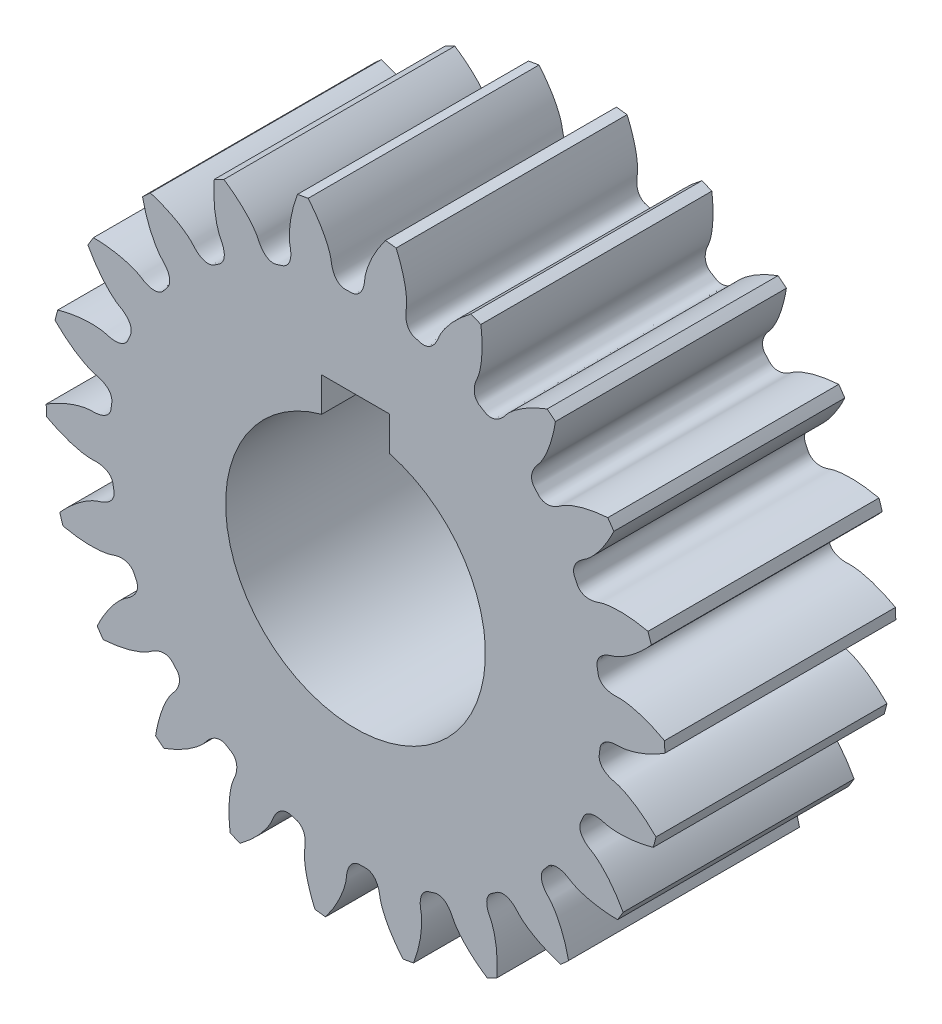
SolidWorks part; units mm, degrees
ref_plane "Front Plane" through (0, 0, 0) normal (0, 0, 1) x (1, 0, 0)
ref_plane "Top Plane" through (0, 0, 0) normal (0, 1, 0) x (1, 0, 0)
ref_plane "Right Plane" through (0, 0, 0) normal (1, 0, 0) x (0, 0, -1)
sketch "Sketch1" plane through (0, 0, 0) normal (0, 0, 1) x (1, 0, 0)
  line L0 (0, -4) -> (0, 4.9154) construction
  line L1 (-1.0414, 4.9154) -> (1.0414, 4.9154)
  line L2 (-1.0414, 4.9154) -> (-1.0414, 3.8621)
  line L3 (1.0414, 4.9154) -> (1.0414, 3.8621)
  arc A1 (-1.4616, 9.4122) -> (-1.7864, 9.356) centre (0, 0) ccw
  arc A20 (-1.0414, 3.8621) -> (1.0414, 3.8621) centre (0, 0) ccw
  arc A22 (1.2494, 9.4427) -> (0.9219, 9.4803) centre (0, 0) ccw
  arc A23 (3.8591, 8.7082) -> (3.5554, 8.8366) centre (0, 0) ccw
  arc A24 (6.1561, 7.2683) -> (5.9009, 7.4769) centre (0, 0) ccw
  arc A25 (7.9545, 5.2395) -> (7.7684, 5.5116) centre (0, 0) ccw
  arc A26 (9.1084, 2.7862) -> (9.0065, 3.0997) centre (0, 0) ccw
  arc A27 (9.5244, 0.1072) -> (9.515, 0.4367) centre (0, 0) ccw
  arc A28 (9.1688, -2.5805) -> (9.2526, -2.2617) centre (0, 0) ccw
  arc A29 (8.0704, -5.0591) -> (8.2406, -4.7768) centre (0, 0) ccw
  arc A30 (6.3182, -7.1279) -> (6.561, -6.905) centre (0, 0) ccw
  arc A31 (4.0541, -8.6192) -> (4.3499, -8.4737) centre (0, 0) ccw
  arc A32 (1.4616, -9.4122) -> (1.7864, -9.356) centre (0, 0) ccw
  arc A33 (-1.2494, -9.4427) -> (-0.9219, -9.4803) centre (0, 0) ccw
  arc A34 (-3.8591, -8.7082) -> (-3.5554, -8.8366) centre (0, 0) ccw
  arc A35 (-6.1561, -7.2683) -> (-5.9009, -7.4769) centre (0, 0) ccw
  arc A36 (-7.9545, -5.2395) -> (-7.7684, -5.5116) centre (0, 0) ccw
  arc A37 (-9.1084, -2.7862) -> (-9.0065, -3.0997) centre (0, 0) ccw
  arc A38 (-9.5244, -0.1072) -> (-9.515, -0.4367) centre (0, 0) ccw
  arc A39 (-9.1688, 2.5805) -> (-9.2526, 2.2617) centre (0, 0) ccw
  arc A40 (-8.0704, 5.0591) -> (-8.2406, 4.7768) centre (0, 0) ccw
  arc A41 (-6.3182, 7.1279) -> (-6.561, 6.905) centre (0, 0) ccw
  arc A42 (-4.0541, 8.6192) -> (-4.3499, 8.4737) centre (0, 0) ccw
  spline S0 degree 3 poles (0.9219, 9.4803) (0.8728, 9.4149) (0.7991, 9.3114) (0.7064, 9.1689) (0.6396, 9.0591) (0.5802, 8.954) (0.5276, 8.8541) (0.4816, 8.7596) (0.4417, 8.6708) (0.4075, 8.588) (0.3787, 8.5115) (0.3547, 8.4415) (0.3352, 8.3782) (0.3197, 8.3219) (0.3078, 8.2727) (0.299, 8.2308) (0.2929, 8.1963) (0.2845, 8.1391) (0.282, 8.0848) (0.2743, 8.0322) (0.2704, 8.0084) (0.2632, 7.9701) (0.2525, 7.9254) (0.2368, 7.875) (0.221, 7.8334) (0.2024, 7.7931) (0.1806, 7.7538) (0.1547, 7.7156) (0.1237, 7.6787) (0.0864, 7.6435) (0.0417, 7.6116) (-0.0017, 7.5901) (-0.0401, 7.5768) (-0.0711, 7.5693) (-0.1009, 7.565) (-0.1493, 7.5621) (-0.216, 7.5625) (-0.2826, 7.5583) (-0.3311, 7.5584) (-0.3611, 7.561) (-0.3925, 7.5667) (-0.4317, 7.5778) (-0.4761, 7.5968) (-0.5227, 7.6261) (-0.5619, 7.6591) (-0.5949, 7.6942) (-0.6229, 7.7309) (-0.647, 7.7688) (-0.6713, 7.8146) (-0.6948, 7.8696) (-0.7113, 7.9198) (-0.7214, 7.9569) (-0.7272, 7.9799) (-0.7324, 8.0034) (-0.7431, 8.0555) (-0.7487, 8.1096) (-0.7604, 8.1662) (-0.7684, 8.2003) (-0.7796, 8.2417) (-0.7943, 8.2901) (-0.813, 8.3454) (-0.836, 8.4075) (-0.8639, 8.476) (-0.8971, 8.5507) (-0.936, 8.6314) (-0.9809, 8.7178) (-1.0322, 8.8095) (-1.0904, 8.9063) (-1.1558, 9.0078) (-1.2286, 9.1136) (-1.3293, 9.2506) (-1.4089, 9.3497) (-1.4616, 9.4122) knots -1.711873 -1.711873 -1.711873 -1.711873 -1.623296 -1.57405 -1.527618 -1.484001 -1.443197 -1.405207 -1.370031 -1.337669 -1.308122 -1.281388 -1.257469 -1.236363 -1.218072 -1.202595 -1.189931 -1.180082 -1.139962 -1.131119 -1.122418 -1.11385 -1.088841 -1.072621 -1.056613 -1.04065 -1.024521 -1.007966 -0.990676 -0.97231 -0.952557 -0.931244 -0.920025 -0.908493 -0.896727 -0.887452 -0.855936 -0.82442 -0.815146 -0.803379 -0.791848 -0.780629 -0.759316 -0.739562 -0.721197 -0.703907 -0.687352 -0.671223 -0.655259 -0.631177 -0.606467 -0.598023 -0.589455 -0.580754 -0.57191 -0.531791 -0.521942 -0.509278 -0.493801 -0.47551 -0.454404 -0.430485 -0.403751 -0.374203 -0.341842 -0.306666 -0.268676 -0.227872 -0.184254 -0.137822 -0.088576 0 0 0 0
  spline S1 degree 3 poles (-1.7864, 9.356) (-1.815, 9.2795) (-1.8566, 9.1593) (-1.9054, 8.9965) (-1.9385, 8.8723) (-1.966, 8.7548) (-1.9882, 8.6441) (-2.0058, 8.5404) (-2.0191, 8.444) (-2.0285, 8.3549) (-2.0347, 8.2734) (-2.0379, 8.1995) (-2.0388, 8.1333) (-2.0378, 8.0749) (-2.0353, 8.0243) (-2.032, 7.9816) (-2.0281, 7.9468) (-2.0201, 7.8896) (-2.0072, 7.8368) (-1.9997, 7.7841) (-1.9968, 7.7602) (-1.9929, 7.7214) (-1.9905, 7.6755) (-1.9914, 7.6227) (-1.9949, 7.5784) (-2.0013, 7.5344) (-2.0112, 7.4906) (-2.0253, 7.4467) (-2.0446, 7.4025) (-2.0705, 7.3583) (-2.1045, 7.3151) (-2.14, 7.2821) (-2.1731, 7.2586) (-2.2007, 7.2426) (-2.2281, 7.2301) (-2.2738, 7.2138) (-2.3379, 7.1953) (-2.4006, 7.1725) (-2.4472, 7.159) (-2.4767, 7.153) (-2.5084, 7.1497) (-2.5491, 7.1492) (-2.5971, 7.155) (-2.65, 7.17) (-2.6969, 7.1905) (-2.7385, 7.215) (-2.7757, 7.2422) (-2.8095, 7.2718) (-2.8458, 7.3089) (-2.8838, 7.3551) (-2.9137, 7.3986) (-2.9339, 7.4313) (-2.9459, 7.4518) (-2.9576, 7.4729) (-2.9825, 7.5199) (-3.0031, 7.5702) (-3.0302, 7.6212) (-3.0476, 7.6516) (-3.07, 7.6882) (-3.0977, 7.7305) (-3.1312, 7.7784) (-3.1708, 7.8314) (-3.2169, 7.8893) (-3.2698, 7.9516) (-3.3298, 8.0181) (-3.3972, 8.0883) (-3.4723, 8.1619) (-3.5554, 8.2383) (-3.6467, 8.3173) (-3.7465, 8.3983) (-3.8817, 8.5013) (-3.986, 8.5741) (-4.0541, 8.6192) knots -1.711873 -1.711873 -1.711873 -1.711873 -1.623296 -1.57405 -1.527618 -1.484001 -1.443197 -1.405207 -1.370031 -1.337669 -1.308122 -1.281388 -1.257469 -1.236363 -1.218072 -1.202595 -1.189931 -1.180082 -1.139962 -1.131119 -1.122418 -1.11385 -1.088841 -1.072621 -1.056613 -1.04065 -1.024521 -1.007966 -0.990676 -0.97231 -0.952557 -0.931244 -0.920025 -0.908493 -0.896727 -0.887452 -0.855936 -0.82442 -0.815146 -0.803379 -0.791848 -0.780629 -0.759316 -0.739562 -0.721197 -0.703907 -0.687352 -0.671223 -0.655259 -0.631177 -0.606467 -0.598023 -0.589455 -0.580754 -0.57191 -0.531791 -0.521942 -0.509278 -0.493801 -0.47551 -0.454404 -0.430485 -0.403751 -0.374203 -0.341842 -0.306666 -0.268676 -0.227872 -0.184254 -0.137822 -0.088576 0 0 0 0
  spline S2 degree 3 poles (3.5554, 8.8366) (3.49, 8.7877) (3.39, 8.7091) (3.2609, 8.5985) (3.166, 8.5119) (3.0793, 8.4279) (3.0007, 8.3468) (2.9299, 8.2691) (2.8666, 8.1951) (2.8105, 8.1253) (2.7613, 8.06) (2.7186, 7.9996) (2.682, 7.9444) (2.6513, 7.8948) (2.6261, 7.8509) (2.6058, 7.8132) (2.5902, 7.7818) (2.566, 7.7293) (2.5483, 7.6779) (2.5261, 7.6295) (2.5157, 7.6078) (2.4979, 7.5731) (2.4751, 7.5332) (2.4458, 7.4893) (2.419, 7.4538) (2.3898, 7.4204) (2.3578, 7.3889) (2.3222, 7.3595) (2.282, 7.3328) (2.2364, 7.3096) (2.1844, 7.2916) (2.1368, 7.2831) (2.0961, 7.2812) (2.0643, 7.2827) (2.0345, 7.287) (1.9872, 7.2979) (1.9233, 7.317) (1.8582, 7.3318) (1.8117, 7.3456) (1.7837, 7.3564) (1.7552, 7.3708) (1.7207, 7.3924) (1.6834, 7.4233) (1.647, 7.4645) (1.6187, 7.5071) (1.5969, 7.5502) (1.5803, 7.5932) (1.5679, 7.6364) (1.5575, 7.6872) (1.5505, 7.7466) (1.5488, 7.7994) (1.5495, 7.8378) (1.5505, 7.8615) (1.5521, 7.8856) (1.5565, 7.9386) (1.5664, 7.9921) (1.5711, 8.0496) (1.573, 8.0846) (1.5739, 8.1275) (1.5735, 8.1781) (1.5712, 8.2364) (1.5665, 8.3025) (1.559, 8.3761) (1.5482, 8.4571) (1.5337, 8.5455) (1.515, 8.641) (1.4915, 8.7435) (1.463, 8.8527) (1.4288, 8.9685) (1.3887, 9.0906) (1.3307, 9.2504) (1.2823, 9.3679) (1.2494, 9.4427) knots -1.711873 -1.711873 -1.711873 -1.711873 -1.623296 -1.57405 -1.527618 -1.484001 -1.443197 -1.405207 -1.370031 -1.337669 -1.308122 -1.281388 -1.257469 -1.236363 -1.218072 -1.202595 -1.189931 -1.180082 -1.139962 -1.131119 -1.122418 -1.11385 -1.088841 -1.072621 -1.056613 -1.04065 -1.024521 -1.007966 -0.990676 -0.97231 -0.952557 -0.931244 -0.920025 -0.908493 -0.896727 -0.887452 -0.855936 -0.82442 -0.815146 -0.803379 -0.791848 -0.780629 -0.759316 -0.739562 -0.721197 -0.703907 -0.687352 -0.671223 -0.655259 -0.631177 -0.606467 -0.598023 -0.589455 -0.580754 -0.57191 -0.531791 -0.521942 -0.509278 -0.493801 -0.47551 -0.454404 -0.430485 -0.403751 -0.374203 -0.341842 -0.306666 -0.268676 -0.227872 -0.184254 -0.137822 -0.088576 0 0 0 0
  spline S3 degree 3 poles (5.9009, 7.4769) (5.8244, 7.4485) (5.7063, 7.4012) (5.5513, 7.3315) (5.4358, 7.2752) (5.329, 7.2189) (5.2307, 7.1633) (5.1409, 7.1087) (5.0593, 7.0555) (4.9858, 7.0044) (4.9202, 6.9556) (4.8622, 6.9097) (4.8116, 6.867) (4.7681, 6.828) (4.7315, 6.793) (4.7015, 6.7625) (4.6777, 6.7368) (4.6397, 6.6933) (4.6082, 6.6489) (4.5733, 6.6088) (4.5572, 6.5909) (4.5304, 6.5626) (4.4972, 6.5307) (4.4567, 6.4968) (4.421, 6.4704) (4.3835, 6.4465) (4.344, 6.4253) (4.3015, 6.4072) (4.2555, 6.3928) (4.2051, 6.3834) (4.1502, 6.3808) (4.1021, 6.3861) (4.0626, 6.3957) (4.0324, 6.4061) (4.0051, 6.4187) (3.9628, 6.4424) (3.9068, 6.4788) (3.8486, 6.5113) (3.8078, 6.5376) (3.784, 6.5559) (3.7607, 6.5777) (3.7337, 6.6082) (3.7066, 6.6483) (3.6833, 6.6981) (3.6681, 6.747) (3.6594, 6.7944) (3.6556, 6.8404) (3.6558, 6.8853) (3.6601, 6.937) (3.6701, 6.996) (3.6834, 7.0471) (3.6949, 7.0838) (3.7025, 7.1063) (3.7108, 7.1289) (3.73, 7.1785) (3.7546, 7.227) (3.7753, 7.2809) (3.787, 7.314) (3.7999, 7.3548) (3.8138, 7.4035) (3.828, 7.4602) (3.8421, 7.5248) (3.8557, 7.5976) (3.8682, 7.6784) (3.8791, 7.7672) (3.888, 7.8642) (3.8944, 7.9691) (3.8978, 8.082) (3.8977, 8.2027) (3.8936, 8.3311) (3.8829, 8.5007) (3.8696, 8.6272) (3.8591, 8.7082) knots -1.711873 -1.711873 -1.711873 -1.711873 -1.623296 -1.57405 -1.527618 -1.484001 -1.443197 -1.405207 -1.370031 -1.337669 -1.308122 -1.281388 -1.257469 -1.236363 -1.218072 -1.202595 -1.189931 -1.180082 -1.139962 -1.131119 -1.122418 -1.11385 -1.088841 -1.072621 -1.056613 -1.04065 -1.024521 -1.007966 -0.990676 -0.97231 -0.952557 -0.931244 -0.920025 -0.908493 -0.896727 -0.887452 -0.855936 -0.82442 -0.815146 -0.803379 -0.791848 -0.780629 -0.759316 -0.739562 -0.721197 -0.703907 -0.687352 -0.671223 -0.655259 -0.631177 -0.606467 -0.598023 -0.589455 -0.580754 -0.57191 -0.531791 -0.521942 -0.509278 -0.493801 -0.47551 -0.454404 -0.430485 -0.403751 -0.374203 -0.341842 -0.306666 -0.268676 -0.227872 -0.184254 -0.137822 -0.088576 0 0 0 0
  spline S4 degree 3 poles (7.7684, 5.5116) (7.6869, 5.5058) (7.5603, 5.4938) (7.392, 5.4705) (7.2653, 5.449) (7.1469, 5.4252) (7.037, 5.3995) (6.9354, 5.3723) (6.8422, 5.3444) (6.7572, 5.316) (6.6805, 5.2877) (6.6119, 5.2599) (6.5514, 5.2333) (6.4987, 5.2081) (6.4537, 5.1848) (6.4163, 5.164) (6.3862, 5.1461) (6.3374, 5.115) (6.2948, 5.0813) (6.25, 5.0526) (6.2294, 5.04) (6.1957, 5.0204) (6.155, 4.9992) (6.1066, 4.9781) (6.0648, 4.9628) (6.0222, 4.9504) (5.9782, 4.9412) (5.9324, 4.9358) (5.8842, 4.935) (5.8332, 4.9401) (5.7798, 4.9531) (5.7351, 4.9717) (5.6999, 4.9921) (5.6739, 5.0106) (5.6512, 5.0303) (5.6173, 5.065) (5.5739, 5.1156) (5.5271, 5.1633) (5.4954, 5.2) (5.4777, 5.2243) (5.4615, 5.2518) (5.4442, 5.2886) (5.4295, 5.3347) (5.4212, 5.3891) (5.4204, 5.4403) (5.4253, 5.4882) (5.4347, 5.5334) (5.4476, 5.5765) (5.4663, 5.6248) (5.4924, 5.6786) (5.5196, 5.7239) (5.541, 5.7559) (5.5546, 5.7753) (5.569, 5.7947) (5.6014, 5.8368) (5.6386, 5.8765) (5.6737, 5.9224) (5.6942, 5.9508) (5.7181, 5.9863) (5.7451, 6.0292) (5.7747, 6.0795) (5.8065, 6.1376) (5.84, 6.2035) (5.8747, 6.2775) (5.9103, 6.3597) (5.9461, 6.4502) (5.9818, 6.5491) (6.0169, 6.6565) (6.0508, 6.7723) (6.083, 6.8967) (6.1206, 7.0625) (6.1434, 7.1876) (6.1561, 7.2683) knots -1.711873 -1.711873 -1.711873 -1.711873 -1.623296 -1.57405 -1.527618 -1.484001 -1.443197 -1.405207 -1.370031 -1.337669 -1.308122 -1.281388 -1.257469 -1.236363 -1.218072 -1.202595 -1.189931 -1.180082 -1.139962 -1.131119 -1.122418 -1.11385 -1.088841 -1.072621 -1.056613 -1.04065 -1.024521 -1.007966 -0.990676 -0.97231 -0.952557 -0.931244 -0.920025 -0.908493 -0.896727 -0.887452 -0.855936 -0.82442 -0.815146 -0.803379 -0.791848 -0.780629 -0.759316 -0.739562 -0.721197 -0.703907 -0.687352 -0.671223 -0.655259 -0.631177 -0.606467 -0.598023 -0.589455 -0.580754 -0.57191 -0.531791 -0.521942 -0.509278 -0.493801 -0.47551 -0.454404 -0.430485 -0.403751 -0.374203 -0.341842 -0.306666 -0.268676 -0.227872 -0.184254 -0.137822 -0.088576 0 0 0 0
  spline S5 degree 3 poles (9.0065, 3.0997) (8.9267, 3.1171) (8.8018, 3.1412) (8.6338, 3.1664) (8.5061, 3.1814) (8.3859, 3.1919) (8.2731, 3.1982) (8.168, 3.2008) (8.0707, 3.2002) (7.9812, 3.1969) (7.8996, 3.1914) (7.826, 3.1841) (7.7604, 3.1755) (7.7027, 3.1662) (7.653, 3.1566) (7.6112, 3.1472) (7.5773, 3.1384) (7.5218, 3.1223) (7.4714, 3.1021) (7.4203, 3.0872) (7.397, 3.0808) (7.3592, 3.0715) (7.3141, 3.0626) (7.2617, 3.056) (7.2173, 3.0531) (7.1729, 3.0532) (7.1282, 3.0568) (7.0827, 3.0645) (7.0362, 3.0773) (6.9887, 3.0966) (6.9411, 3.1241) (6.9035, 3.1545) (6.8754, 3.184) (6.8557, 3.2091) (6.8395, 3.2344) (6.8167, 3.2773) (6.7893, 3.3381) (6.7579, 3.3969) (6.7378, 3.4411) (6.7277, 3.4694) (6.7199, 3.5003) (6.7137, 3.5406) (6.7125, 3.589) (6.7199, 3.6434) (6.7335, 3.6928) (6.7518, 3.7374) (6.7735, 3.7782) (6.798, 3.8158) (6.8295, 3.857) (6.8698, 3.9011) (6.9086, 3.937) (6.9382, 3.9617) (6.9567, 3.9764) (6.9759, 3.991) (7.0189, 4.0223) (7.0658, 4.0499) (7.1124, 4.084) (7.14, 4.1055) (7.173, 4.1329) (7.211, 4.1663) (7.2536, 4.2063) (7.3004, 4.2531) (7.3511, 4.3069) (7.4053, 4.3682) (7.4626, 4.437) (7.5225, 4.5137) (7.5846, 4.5986) (7.6485, 4.6917) (7.7137, 4.7933) (7.7796, 4.9035) (7.8624, 5.052) (7.9196, 5.1656) (7.9545, 5.2395) knots -1.711873 -1.711873 -1.711873 -1.711873 -1.623296 -1.57405 -1.527618 -1.484001 -1.443197 -1.405207 -1.370031 -1.337669 -1.308122 -1.281388 -1.257469 -1.236363 -1.218072 -1.202595 -1.189931 -1.180082 -1.139962 -1.131119 -1.122418 -1.11385 -1.088841 -1.072621 -1.056613 -1.04065 -1.024521 -1.007966 -0.990676 -0.97231 -0.952557 -0.931244 -0.920025 -0.908493 -0.896727 -0.887452 -0.855936 -0.82442 -0.815146 -0.803379 -0.791848 -0.780629 -0.759316 -0.739562 -0.721197 -0.703907 -0.687352 -0.671223 -0.655259 -0.631177 -0.606467 -0.598023 -0.589455 -0.580754 -0.57191 -0.531791 -0.521942 -0.509278 -0.493801 -0.47551 -0.454404 -0.430485 -0.403751 -0.374203 -0.341842 -0.306666 -0.268676 -0.227872 -0.184254 -0.137822 -0.088576 0 0 0 0
  spline S6 degree 3 poles (9.515, 0.4367) (9.4433, 0.4759) (9.3303, 0.5342) (9.1761, 0.6057) (9.0579, 0.6561) (8.9455, 0.7) (8.8391, 0.7378) (8.739, 0.7699) (8.6454, 0.7968) (8.5586, 0.8188) (8.4788, 0.8365) (8.4061, 0.8503) (8.3407, 0.8606) (8.2827, 0.8679) (8.2323, 0.8726) (8.1896, 0.8754) (8.1546, 0.8765) (8.0968, 0.8767) (8.0427, 0.8715) (7.9895, 0.8716) (7.9654, 0.8721) (7.9264, 0.8738) (7.8807, 0.8779) (7.8285, 0.8863) (7.7851, 0.8961) (7.7426, 0.9087) (7.7006, 0.9247) (7.6591, 0.945) (7.6181, 0.9703) (7.578, 1.0022) (7.5401, 1.042) (7.5126, 1.0818) (7.494, 1.118) (7.4821, 1.1476) (7.4737, 1.1765) (7.4639, 1.224) (7.4547, 1.2901) (7.4412, 1.3554) (7.4344, 1.4034) (7.4326, 1.4335) (7.4339, 1.4653) (7.4392, 1.5057) (7.4518, 1.5524) (7.4741, 1.6027) (7.5012, 1.6462) (7.5313, 1.6838) (7.5635, 1.7168) (7.5977, 1.746) (7.6395, 1.7766) (7.6906, 1.8077) (7.738, 1.8311) (7.7732, 1.8465) (7.7952, 1.8554) (7.8177, 1.864) (7.8678, 1.8819) (7.9205, 1.8952) (7.9749, 1.9148) (8.0075, 1.9276) (8.0468, 1.9446) (8.0927, 1.966) (8.1448, 1.9924) (8.2029, 2.024) (8.2668, 2.0614) (8.336, 2.1049) (8.4104, 2.1548) (8.4895, 2.2116) (8.573, 2.2754) (8.6605, 2.3468) (8.7516, 2.4259) (8.846, 2.5131) (8.9672, 2.6323) (9.0541, 2.7252) (9.1084, 2.7862) knots -1.711873 -1.711873 -1.711873 -1.711873 -1.623296 -1.57405 -1.527618 -1.484001 -1.443197 -1.405207 -1.370031 -1.337669 -1.308122 -1.281388 -1.257469 -1.236363 -1.218072 -1.202595 -1.189931 -1.180082 -1.139962 -1.131119 -1.122418 -1.11385 -1.088841 -1.072621 -1.056613 -1.04065 -1.024521 -1.007966 -0.990676 -0.97231 -0.952557 -0.931244 -0.920025 -0.908493 -0.896727 -0.887452 -0.855936 -0.82442 -0.815146 -0.803379 -0.791848 -0.780629 -0.759316 -0.739562 -0.721197 -0.703907 -0.687352 -0.671223 -0.655259 -0.631177 -0.606467 -0.598023 -0.589455 -0.580754 -0.57191 -0.531791 -0.521942 -0.509278 -0.493801 -0.47551 -0.454404 -0.430485 -0.403751 -0.374203 -0.341842 -0.306666 -0.268676 -0.227872 -0.184254 -0.137822 -0.088576 0 0 0 0
  spline S7 degree 3 poles (9.2526, -2.2617) (9.1949, -2.2038) (9.1029, -2.1161) (8.975, -2.004) (8.8758, -1.9224) (8.7803, -1.8486) (8.6889, -1.7823) (8.6019, -1.7233) (8.5197, -1.6712) (8.4426, -1.6256) (8.371, -1.5861) (8.3051, -1.5524) (8.2453, -1.5241) (8.1917, -1.5008) (8.1447, -1.482) (8.1045, -1.4674) (8.0712, -1.4564) (8.0158, -1.4399) (7.9624, -1.4297) (7.9114, -1.4146) (7.8884, -1.4074) (7.8515, -1.3948) (7.8088, -1.3779) (7.7611, -1.3551) (7.7222, -1.3335) (7.6849, -1.3094) (7.6492, -1.2822) (7.6151, -1.2512) (7.5829, -1.2152) (7.5534, -1.1733) (7.5282, -1.1245) (7.513, -1.0785) (7.5054, -1.0386) (7.5023, -1.0068) (7.5024, -0.9767) (7.5064, -0.9284) (7.5162, -0.8624) (7.5216, -0.7959) (7.5286, -0.7479) (7.5354, -0.7186) (7.5456, -0.6884) (7.5621, -0.6512) (7.5873, -0.6098) (7.6229, -0.568) (7.6611, -0.5339) (7.7006, -0.5062) (7.7408, -0.4836) (7.7818, -0.4652) (7.8306, -0.4476) (7.8884, -0.4322) (7.9404, -0.4231) (7.9786, -0.4183) (8.0022, -0.4159) (8.0262, -0.414) (8.0793, -0.4109) (8.1336, -0.4131) (8.1913, -0.4096) (8.2262, -0.4064) (8.2687, -0.4012) (8.3188, -0.3936) (8.3762, -0.383) (8.4409, -0.369) (8.5127, -0.3511) (8.5914, -0.3289) (8.6768, -0.3019) (8.7687, -0.2698) (8.8668, -0.232) (8.9708, -0.1882) (9.0806, -0.1379) (9.1957, -0.0809) (9.3456, -0.0007) (9.4551, 0.0639) (9.5244, 0.1072) knots -1.711873 -1.711873 -1.711873 -1.711873 -1.623296 -1.57405 -1.527618 -1.484001 -1.443197 -1.405207 -1.370031 -1.337669 -1.308122 -1.281388 -1.257469 -1.236363 -1.218072 -1.202595 -1.189931 -1.180082 -1.139962 -1.131119 -1.122418 -1.11385 -1.088841 -1.072621 -1.056613 -1.04065 -1.024521 -1.007966 -0.990676 -0.97231 -0.952557 -0.931244 -0.920025 -0.908493 -0.896727 -0.887452 -0.855936 -0.82442 -0.815146 -0.803379 -0.791848 -0.780629 -0.759316 -0.739562 -0.721197 -0.703907 -0.687352 -0.671223 -0.655259 -0.631177 -0.606467 -0.598023 -0.589455 -0.580754 -0.57191 -0.531791 -0.521942 -0.509278 -0.493801 -0.47551 -0.454404 -0.430485 -0.403751 -0.374203 -0.341842 -0.306666 -0.268676 -0.227872 -0.184254 -0.137822 -0.088576 0 0 0 0
  spline S8 degree 3 poles (8.2406, -4.7768) (8.2015, -4.7051) (8.138, -4.5949) (8.0469, -4.4514) (7.9747, -4.3451) (7.9039, -4.2474) (7.8348, -4.1581) (7.7679, -4.0769) (7.7037, -4.0037) (7.6426, -3.9383) (7.585, -3.8802) (7.5313, -3.8294) (7.4819, -3.7854) (7.4371, -3.7479) (7.3973, -3.7166) (7.3628, -3.6912) (7.3339, -3.6713) (7.2854, -3.6399) (7.2371, -3.6151) (7.1924, -3.5862) (7.1724, -3.5728) (7.1405, -3.5503) (7.1043, -3.522) (7.065, -3.4868) (7.0337, -3.4551) (7.0047, -3.4215) (6.9781, -3.3853) (6.9541, -3.3459) (6.9334, -3.3024) (6.9169, -3.2539) (6.9065, -3.1999) (6.9048, -3.1515) (6.9088, -3.111) (6.9148, -3.0797) (6.9233, -3.0508) (6.9408, -3.0056) (6.9688, -2.945) (6.9927, -2.8827) (7.013, -2.8387) (7.0277, -2.8125) (7.046, -2.7863) (7.0723, -2.7553) (7.1081, -2.7227) (7.1541, -2.6926) (7.2004, -2.6706) (7.2461, -2.6552) (7.291, -2.6449) (7.3355, -2.6388) (7.3873, -2.6356) (7.4471, -2.6371) (7.4996, -2.643) (7.5375, -2.6492) (7.5609, -2.6535) (7.5844, -2.6585) (7.6363, -2.6705) (7.6878, -2.6878) (7.7441, -2.7007) (7.7785, -2.7075) (7.8207, -2.7146) (7.8709, -2.7213) (7.929, -2.7273) (7.995, -2.7321) (8.0689, -2.7352) (8.1507, -2.7361) (8.2402, -2.7342) (8.3375, -2.7293) (8.4422, -2.7207) (8.5544, -2.7079) (8.6739, -2.6906) (8.8004, -2.6683) (8.9668, -2.6336) (9.0901, -2.6025) (9.1688, -2.5805) knots -1.711873 -1.711873 -1.711873 -1.711873 -1.623296 -1.57405 -1.527618 -1.484001 -1.443197 -1.405207 -1.370031 -1.337669 -1.308122 -1.281388 -1.257469 -1.236363 -1.218072 -1.202595 -1.189931 -1.180082 -1.139962 -1.131119 -1.122418 -1.11385 -1.088841 -1.072621 -1.056613 -1.04065 -1.024521 -1.007966 -0.990676 -0.97231 -0.952557 -0.931244 -0.920025 -0.908493 -0.896727 -0.887452 -0.855936 -0.82442 -0.815146 -0.803379 -0.791848 -0.780629 -0.759316 -0.739562 -0.721197 -0.703907 -0.687352 -0.671223 -0.655259 -0.631177 -0.606467 -0.598023 -0.589455 -0.580754 -0.57191 -0.531791 -0.521942 -0.509278 -0.493801 -0.47551 -0.454404 -0.430485 -0.403751 -0.374203 -0.341842 -0.306666 -0.268676 -0.227872 -0.184254 -0.137822 -0.088576 0 0 0 0
  spline S9 degree 3 poles (6.561, -6.905) (6.5437, -6.8251) (6.5138, -6.7015) (6.4668, -6.5382) (6.4275, -6.4158) (6.3871, -6.3021) (6.346, -6.1969) (6.3047, -6.1003) (6.2637, -6.012) (6.2235, -5.9319) (6.1846, -5.86) (6.1474, -5.7961) (6.1123, -5.7399) (6.0799, -5.6913) (6.0505, -5.6501) (6.0246, -5.616) (6.0025, -5.5888) (5.9649, -5.545) (5.9254, -5.5075) (5.8907, -5.4673) (5.8753, -5.4488) (5.8511, -5.4182) (5.8242, -5.3809) (5.7964, -5.336) (5.7754, -5.2968) (5.7571, -5.2564) (5.7417, -5.2142) (5.7298, -5.1696) (5.7221, -5.122) (5.72, -5.0708) (5.7252, -5.0161) (5.7373, -4.9692) (5.7525, -4.9314) (5.767, -4.9031) (5.7833, -4.8778) (5.8129, -4.8393) (5.8568, -4.7891) (5.8973, -4.7361) (5.9291, -4.6995) (5.9507, -4.6785) (5.9756, -4.6586) (6.0096, -4.6362) (6.0531, -4.615) (6.1057, -4.5991) (6.1563, -4.591) (6.2045, -4.5891) (6.2506, -4.5919) (6.295, -4.5985) (6.3455, -4.6101) (6.4024, -4.6284) (6.4512, -4.6488) (6.4859, -4.6654) (6.507, -4.6762) (6.5282, -4.6876) (6.5746, -4.7137) (6.6191, -4.7449) (6.6695, -4.7731) (6.7006, -4.7893) (6.7392, -4.808) (6.7854, -4.8286) (6.8394, -4.8507) (6.9014, -4.8739) (6.9715, -4.8977) (7.0497, -4.9215) (7.1361, -4.945) (7.2308, -4.9677) (7.3338, -4.9889) (7.445, -5.0083) (7.5645, -5.0254) (7.6922, -5.0396) (7.8616, -5.0532) (7.9887, -5.058) (8.0704, -5.0591) knots -1.711873 -1.711873 -1.711873 -1.711873 -1.623296 -1.57405 -1.527618 -1.484001 -1.443197 -1.405207 -1.370031 -1.337669 -1.308122 -1.281388 -1.257469 -1.236363 -1.218072 -1.202595 -1.189931 -1.180082 -1.139962 -1.131119 -1.122418 -1.11385 -1.088841 -1.072621 -1.056613 -1.04065 -1.024521 -1.007966 -0.990676 -0.97231 -0.952557 -0.931244 -0.920025 -0.908493 -0.896727 -0.887452 -0.855936 -0.82442 -0.815146 -0.803379 -0.791848 -0.780629 -0.759316 -0.739562 -0.721197 -0.703907 -0.687352 -0.671223 -0.655259 -0.631177 -0.606467 -0.598023 -0.589455 -0.580754 -0.57191 -0.531791 -0.521942 -0.509278 -0.493801 -0.47551 -0.454404 -0.430485 -0.403751 -0.374203 -0.341842 -0.306666 -0.268676 -0.227872 -0.184254 -0.137822 -0.088576 0 0 0 0
  spline S10 degree 3 poles (4.3499, -8.4737) (4.3558, -8.3922) (4.3619, -8.2652) (4.3629, -8.0952) (4.3596, -7.9668) (4.3528, -7.8463) (4.343, -7.7338) (4.3307, -7.6294) (4.3162, -7.5331) (4.3002, -7.445) (4.2831, -7.365) (4.2654, -7.2932) (4.2476, -7.2295) (4.2302, -7.1737) (4.2136, -7.1259) (4.1983, -7.0859) (4.1848, -7.0535) (4.161, -7.0009) (4.1338, -6.9538) (4.1118, -6.9054) (4.1022, -6.8833) (4.0876, -6.8472) (4.0723, -6.8038) (4.0583, -6.7529) (4.0492, -6.7094) (4.043, -6.6654) (4.0401, -6.6206) (4.0413, -6.5744) (4.0473, -6.5266) (4.0597, -6.4769) (4.0801, -6.4258) (4.1049, -6.3843) (4.1301, -6.3523) (4.1521, -6.3292) (4.1748, -6.3095) (4.214, -6.281) (4.2703, -6.2452) (4.3241, -6.2057) (4.365, -6.1795) (4.3916, -6.1655) (4.4211, -6.1534) (4.46, -6.1415) (4.5077, -6.1334) (4.5627, -6.133) (4.6135, -6.1395) (4.6603, -6.1512) (4.7037, -6.1668) (4.7444, -6.1857) (4.7896, -6.2111) (4.8391, -6.2447) (4.8801, -6.278) (4.9087, -6.3037) (4.926, -6.32) (4.9431, -6.3369) (4.9803, -6.375) (5.0142, -6.4175) (5.0546, -6.4588) (5.0799, -6.4831) (5.1116, -6.5118) (5.1502, -6.5446) (5.1958, -6.5811) (5.2487, -6.6208) (5.3093, -6.6634) (5.3776, -6.7083) (5.4539, -6.7552) (5.5384, -6.8036) (5.6312, -6.853) (5.7324, -6.9029) (5.8423, -6.953) (5.9608, -7.0026) (6.1195, -7.0634) (6.2401, -7.1038) (6.3182, -7.1279) knots -1.711873 -1.711873 -1.711873 -1.711873 -1.623296 -1.57405 -1.527618 -1.484001 -1.443197 -1.405207 -1.370031 -1.337669 -1.308122 -1.281388 -1.257469 -1.236363 -1.218072 -1.202595 -1.189931 -1.180082 -1.139962 -1.131119 -1.122418 -1.11385 -1.088841 -1.072621 -1.056613 -1.04065 -1.024521 -1.007966 -0.990676 -0.97231 -0.952557 -0.931244 -0.920025 -0.908493 -0.896727 -0.887452 -0.855936 -0.82442 -0.815146 -0.803379 -0.791848 -0.780629 -0.759316 -0.739562 -0.721197 -0.703907 -0.687352 -0.671223 -0.655259 -0.631177 -0.606467 -0.598023 -0.589455 -0.580754 -0.57191 -0.531791 -0.521942 -0.509278 -0.493801 -0.47551 -0.454404 -0.430485 -0.403751 -0.374203 -0.341842 -0.306666 -0.268676 -0.227872 -0.184254 -0.137822 -0.088576 0 0 0 0
  spline S11 degree 3 poles (1.7864, -9.356) (1.815, -9.2795) (1.8566, -9.1593) (1.9054, -8.9965) (1.9385, -8.8723) (1.966, -8.7548) (1.9882, -8.6441) (2.0058, -8.5404) (2.0191, -8.444) (2.0285, -8.3549) (2.0347, -8.2734) (2.0379, -8.1995) (2.0388, -8.1333) (2.0378, -8.0749) (2.0353, -8.0243) (2.032, -7.9816) (2.0281, -7.9468) (2.0201, -7.8896) (2.0072, -7.8368) (1.9997, -7.7841) (1.9968, -7.7602) (1.9929, -7.7214) (1.9905, -7.6755) (1.9914, -7.6227) (1.9949, -7.5784) (2.0013, -7.5344) (2.0112, -7.4906) (2.0253, -7.4467) (2.0446, -7.4025) (2.0705, -7.3583) (2.1045, -7.3151) (2.14, -7.2821) (2.1731, -7.2586) (2.2007, -7.2426) (2.2281, -7.2301) (2.2738, -7.2138) (2.3379, -7.1953) (2.4006, -7.1725) (2.4472, -7.159) (2.4767, -7.153) (2.5084, -7.1497) (2.5491, -7.1492) (2.5971, -7.155) (2.65, -7.17) (2.6969, -7.1905) (2.7385, -7.215) (2.7757, -7.2422) (2.8095, -7.2718) (2.8458, -7.3089) (2.8838, -7.3551) (2.9137, -7.3986) (2.9339, -7.4313) (2.9459, -7.4518) (2.9576, -7.4729) (2.9825, -7.5199) (3.0031, -7.5702) (3.0302, -7.6212) (3.0476, -7.6516) (3.07, -7.6882) (3.0977, -7.7305) (3.1312, -7.7784) (3.1708, -7.8314) (3.2169, -7.8893) (3.2698, -7.9516) (3.3298, -8.0181) (3.3972, -8.0883) (3.4723, -8.1619) (3.5554, -8.2383) (3.6467, -8.3173) (3.7465, -8.3983) (3.8817, -8.5013) (3.986, -8.5741) (4.0541, -8.6192) knots -1.711873 -1.711873 -1.711873 -1.711873 -1.623296 -1.57405 -1.527618 -1.484001 -1.443197 -1.405207 -1.370031 -1.337669 -1.308122 -1.281388 -1.257469 -1.236363 -1.218072 -1.202595 -1.189931 -1.180082 -1.139962 -1.131119 -1.122418 -1.11385 -1.088841 -1.072621 -1.056613 -1.04065 -1.024521 -1.007966 -0.990676 -0.97231 -0.952557 -0.931244 -0.920025 -0.908493 -0.896727 -0.887452 -0.855936 -0.82442 -0.815146 -0.803379 -0.791848 -0.780629 -0.759316 -0.739562 -0.721197 -0.703907 -0.687352 -0.671223 -0.655259 -0.631177 -0.606467 -0.598023 -0.589455 -0.580754 -0.57191 -0.531791 -0.521942 -0.509278 -0.493801 -0.47551 -0.454404 -0.430485 -0.403751 -0.374203 -0.341842 -0.306666 -0.268676 -0.227872 -0.184254 -0.137822 -0.088576 0 0 0 0
  spline S12 degree 3 poles (-0.9219, -9.4803) (-0.8728, -9.4149) (-0.7991, -9.3114) (-0.7064, -9.1689) (-0.6396, -9.0591) (-0.5802, -8.954) (-0.5276, -8.8541) (-0.4816, -8.7596) (-0.4417, -8.6708) (-0.4075, -8.588) (-0.3787, -8.5115) (-0.3547, -8.4415) (-0.3352, -8.3782) (-0.3197, -8.3219) (-0.3078, -8.2727) (-0.299, -8.2308) (-0.2929, -8.1963) (-0.2845, -8.1391) (-0.282, -8.0848) (-0.2743, -8.0322) (-0.2704, -8.0084) (-0.2632, -7.9701) (-0.2525, -7.9254) (-0.2368, -7.875) (-0.221, -7.8334) (-0.2024, -7.7931) (-0.1806, -7.7538) (-0.1547, -7.7156) (-0.1237, -7.6787) (-0.0864, -7.6435) (-0.0417, -7.6116) (0.0017, -7.5901) (0.0401, -7.5768) (0.0711, -7.5693) (0.1009, -7.565) (0.1493, -7.5621) (0.216, -7.5625) (0.2826, -7.5583) (0.3311, -7.5584) (0.3611, -7.561) (0.3925, -7.5667) (0.4317, -7.5778) (0.4761, -7.5968) (0.5227, -7.6261) (0.5619, -7.6591) (0.5949, -7.6942) (0.6229, -7.7309) (0.647, -7.7688) (0.6713, -7.8146) (0.6948, -7.8696) (0.7113, -7.9198) (0.7214, -7.9569) (0.7272, -7.9799) (0.7324, -8.0034) (0.7431, -8.0555) (0.7487, -8.1096) (0.7604, -8.1662) (0.7684, -8.2003) (0.7796, -8.2417) (0.7943, -8.2901) (0.813, -8.3454) (0.836, -8.4075) (0.8639, -8.476) (0.8971, -8.5507) (0.936, -8.6314) (0.9809, -8.7178) (1.0322, -8.8095) (1.0904, -8.9063) (1.1558, -9.0078) (1.2286, -9.1136) (1.3293, -9.2506) (1.4089, -9.3497) (1.4616, -9.4122) knots -1.711873 -1.711873 -1.711873 -1.711873 -1.623296 -1.57405 -1.527618 -1.484001 -1.443197 -1.405207 -1.370031 -1.337669 -1.308122 -1.281388 -1.257469 -1.236363 -1.218072 -1.202595 -1.189931 -1.180082 -1.139962 -1.131119 -1.122418 -1.11385 -1.088841 -1.072621 -1.056613 -1.04065 -1.024521 -1.007966 -0.990676 -0.97231 -0.952557 -0.931244 -0.920025 -0.908493 -0.896727 -0.887452 -0.855936 -0.82442 -0.815146 -0.803379 -0.791848 -0.780629 -0.759316 -0.739562 -0.721197 -0.703907 -0.687352 -0.671223 -0.655259 -0.631177 -0.606467 -0.598023 -0.589455 -0.580754 -0.57191 -0.531791 -0.521942 -0.509278 -0.493801 -0.47551 -0.454404 -0.430485 -0.403751 -0.374203 -0.341842 -0.306666 -0.268676 -0.227872 -0.184254 -0.137822 -0.088576 0 0 0 0
  spline S13 degree 3 poles (-3.5554, -8.8366) (-3.49, -8.7877) (-3.39, -8.7091) (-3.2609, -8.5985) (-3.166, -8.5119) (-3.0793, -8.4279) (-3.0007, -8.3468) (-2.9299, -8.2691) (-2.8666, -8.1951) (-2.8105, -8.1253) (-2.7613, -8.06) (-2.7186, -7.9996) (-2.682, -7.9444) (-2.6513, -7.8948) (-2.6261, -7.8509) (-2.6058, -7.8132) (-2.5902, -7.7818) (-2.566, -7.7293) (-2.5483, -7.6779) (-2.5261, -7.6295) (-2.5157, -7.6078) (-2.4979, -7.5731) (-2.4751, -7.5332) (-2.4458, -7.4893) (-2.419, -7.4538) (-2.3898, -7.4204) (-2.3578, -7.3889) (-2.3222, -7.3595) (-2.282, -7.3328) (-2.2364, -7.3096) (-2.1844, -7.2916) (-2.1368, -7.2831) (-2.0961, -7.2812) (-2.0643, -7.2827) (-2.0345, -7.287) (-1.9872, -7.2979) (-1.9233, -7.317) (-1.8582, -7.3318) (-1.8117, -7.3456) (-1.7837, -7.3564) (-1.7552, -7.3708) (-1.7207, -7.3924) (-1.6834, -7.4233) (-1.647, -7.4645) (-1.6187, -7.5071) (-1.5969, -7.5502) (-1.5803, -7.5932) (-1.5679, -7.6364) (-1.5575, -7.6872) (-1.5505, -7.7466) (-1.5488, -7.7994) (-1.5495, -7.8378) (-1.5505, -7.8615) (-1.5521, -7.8856) (-1.5565, -7.9386) (-1.5664, -7.9921) (-1.5711, -8.0496) (-1.573, -8.0846) (-1.5739, -8.1275) (-1.5735, -8.1781) (-1.5712, -8.2364) (-1.5665, -8.3025) (-1.559, -8.3761) (-1.5482, -8.4571) (-1.5337, -8.5455) (-1.515, -8.641) (-1.4915, -8.7435) (-1.463, -8.8527) (-1.4288, -8.9685) (-1.3887, -9.0906) (-1.3307, -9.2504) (-1.2823, -9.3679) (-1.2494, -9.4427) knots -1.711873 -1.711873 -1.711873 -1.711873 -1.623296 -1.57405 -1.527618 -1.484001 -1.443197 -1.405207 -1.370031 -1.337669 -1.308122 -1.281388 -1.257469 -1.236363 -1.218072 -1.202595 -1.189931 -1.180082 -1.139962 -1.131119 -1.122418 -1.11385 -1.088841 -1.072621 -1.056613 -1.04065 -1.024521 -1.007966 -0.990676 -0.97231 -0.952557 -0.931244 -0.920025 -0.908493 -0.896727 -0.887452 -0.855936 -0.82442 -0.815146 -0.803379 -0.791848 -0.780629 -0.759316 -0.739562 -0.721197 -0.703907 -0.687352 -0.671223 -0.655259 -0.631177 -0.606467 -0.598023 -0.589455 -0.580754 -0.57191 -0.531791 -0.521942 -0.509278 -0.493801 -0.47551 -0.454404 -0.430485 -0.403751 -0.374203 -0.341842 -0.306666 -0.268676 -0.227872 -0.184254 -0.137822 -0.088576 0 0 0 0
  spline S14 degree 3 poles (-5.9009, -7.4769) (-5.8244, -7.4485) (-5.7063, -7.4012) (-5.5513, -7.3315) (-5.4358, -7.2752) (-5.329, -7.2189) (-5.2307, -7.1633) (-5.1409, -7.1087) (-5.0593, -7.0555) (-4.9858, -7.0044) (-4.9202, -6.9556) (-4.8622, -6.9097) (-4.8116, -6.867) (-4.7681, -6.828) (-4.7315, -6.793) (-4.7015, -6.7625) (-4.6777, -6.7368) (-4.6397, -6.6933) (-4.6082, -6.6489) (-4.5733, -6.6088) (-4.5572, -6.5909) (-4.5304, -6.5626) (-4.4972, -6.5307) (-4.4567, -6.4968) (-4.421, -6.4704) (-4.3835, -6.4465) (-4.344, -6.4253) (-4.3015, -6.4072) (-4.2555, -6.3928) (-4.2051, -6.3834) (-4.1502, -6.3808) (-4.1021, -6.3861) (-4.0626, -6.3957) (-4.0324, -6.4061) (-4.0051, -6.4187) (-3.9628, -6.4424) (-3.9068, -6.4788) (-3.8486, -6.5113) (-3.8078, -6.5376) (-3.784, -6.5559) (-3.7607, -6.5777) (-3.7337, -6.6082) (-3.7066, -6.6483) (-3.6833, -6.6981) (-3.6681, -6.747) (-3.6594, -6.7944) (-3.6556, -6.8404) (-3.6558, -6.8853) (-3.6601, -6.937) (-3.6701, -6.996) (-3.6834, -7.0471) (-3.6949, -7.0838) (-3.7025, -7.1063) (-3.7108, -7.1289) (-3.73, -7.1785) (-3.7546, -7.227) (-3.7753, -7.2809) (-3.787, -7.314) (-3.7999, -7.3548) (-3.8138, -7.4035) (-3.828, -7.4602) (-3.8421, -7.5248) (-3.8557, -7.5976) (-3.8682, -7.6784) (-3.8791, -7.7672) (-3.888, -7.8642) (-3.8944, -7.9691) (-3.8978, -8.082) (-3.8977, -8.2027) (-3.8936, -8.3311) (-3.8829, -8.5007) (-3.8696, -8.6272) (-3.8591, -8.7082) knots -1.711873 -1.711873 -1.711873 -1.711873 -1.623296 -1.57405 -1.527618 -1.484001 -1.443197 -1.405207 -1.370031 -1.337669 -1.308122 -1.281388 -1.257469 -1.236363 -1.218072 -1.202595 -1.189931 -1.180082 -1.139962 -1.131119 -1.122418 -1.11385 -1.088841 -1.072621 -1.056613 -1.04065 -1.024521 -1.007966 -0.990676 -0.97231 -0.952557 -0.931244 -0.920025 -0.908493 -0.896727 -0.887452 -0.855936 -0.82442 -0.815146 -0.803379 -0.791848 -0.780629 -0.759316 -0.739562 -0.721197 -0.703907 -0.687352 -0.671223 -0.655259 -0.631177 -0.606467 -0.598023 -0.589455 -0.580754 -0.57191 -0.531791 -0.521942 -0.509278 -0.493801 -0.47551 -0.454404 -0.430485 -0.403751 -0.374203 -0.341842 -0.306666 -0.268676 -0.227872 -0.184254 -0.137822 -0.088576 0 0 0 0
  spline S15 degree 3 poles (-7.7684, -5.5116) (-7.6869, -5.5058) (-7.5603, -5.4938) (-7.392, -5.4705) (-7.2653, -5.449) (-7.1469, -5.4252) (-7.037, -5.3995) (-6.9354, -5.3723) (-6.8422, -5.3444) (-6.7572, -5.316) (-6.6805, -5.2877) (-6.6119, -5.2599) (-6.5514, -5.2333) (-6.4987, -5.2081) (-6.4537, -5.1848) (-6.4163, -5.164) (-6.3862, -5.1461) (-6.3374, -5.115) (-6.2948, -5.0813) (-6.25, -5.0526) (-6.2294, -5.04) (-6.1957, -5.0204) (-6.155, -4.9992) (-6.1066, -4.9781) (-6.0648, -4.9628) (-6.0222, -4.9504) (-5.9782, -4.9412) (-5.9324, -4.9358) (-5.8842, -4.935) (-5.8332, -4.9401) (-5.7798, -4.9531) (-5.7351, -4.9717) (-5.6999, -4.9921) (-5.6739, -5.0106) (-5.6512, -5.0303) (-5.6173, -5.065) (-5.5739, -5.1156) (-5.5271, -5.1633) (-5.4954, -5.2) (-5.4777, -5.2243) (-5.4615, -5.2518) (-5.4442, -5.2886) (-5.4295, -5.3347) (-5.4212, -5.3891) (-5.4204, -5.4403) (-5.4253, -5.4882) (-5.4347, -5.5334) (-5.4476, -5.5765) (-5.4663, -5.6248) (-5.4924, -5.6786) (-5.5196, -5.7239) (-5.541, -5.7559) (-5.5546, -5.7753) (-5.569, -5.7947) (-5.6014, -5.8368) (-5.6386, -5.8765) (-5.6737, -5.9224) (-5.6942, -5.9508) (-5.7181, -5.9863) (-5.7451, -6.0292) (-5.7747, -6.0795) (-5.8065, -6.1376) (-5.84, -6.2035) (-5.8747, -6.2775) (-5.9103, -6.3597) (-5.9461, -6.4502) (-5.9818, -6.5491) (-6.0169, -6.6565) (-6.0508, -6.7723) (-6.083, -6.8967) (-6.1206, -7.0625) (-6.1434, -7.1876) (-6.1561, -7.2683) knots -1.711873 -1.711873 -1.711873 -1.711873 -1.623296 -1.57405 -1.527618 -1.484001 -1.443197 -1.405207 -1.370031 -1.337669 -1.308122 -1.281388 -1.257469 -1.236363 -1.218072 -1.202595 -1.189931 -1.180082 -1.139962 -1.131119 -1.122418 -1.11385 -1.088841 -1.072621 -1.056613 -1.04065 -1.024521 -1.007966 -0.990676 -0.97231 -0.952557 -0.931244 -0.920025 -0.908493 -0.896727 -0.887452 -0.855936 -0.82442 -0.815146 -0.803379 -0.791848 -0.780629 -0.759316 -0.739562 -0.721197 -0.703907 -0.687352 -0.671223 -0.655259 -0.631177 -0.606467 -0.598023 -0.589455 -0.580754 -0.57191 -0.531791 -0.521942 -0.509278 -0.493801 -0.47551 -0.454404 -0.430485 -0.403751 -0.374203 -0.341842 -0.306666 -0.268676 -0.227872 -0.184254 -0.137822 -0.088576 0 0 0 0
  spline S16 degree 3 poles (-9.0065, -3.0997) (-8.9267, -3.1171) (-8.8018, -3.1412) (-8.6338, -3.1664) (-8.5061, -3.1814) (-8.3859, -3.1919) (-8.2731, -3.1982) (-8.168, -3.2008) (-8.0707, -3.2002) (-7.9812, -3.1969) (-7.8996, -3.1914) (-7.826, -3.1841) (-7.7604, -3.1755) (-7.7027, -3.1662) (-7.653, -3.1566) (-7.6112, -3.1472) (-7.5773, -3.1384) (-7.5218, -3.1223) (-7.4714, -3.1021) (-7.4203, -3.0872) (-7.397, -3.0808) (-7.3592, -3.0715) (-7.3141, -3.0626) (-7.2617, -3.056) (-7.2173, -3.0531) (-7.1729, -3.0532) (-7.1282, -3.0568) (-7.0827, -3.0645) (-7.0362, -3.0773) (-6.9887, -3.0966) (-6.9411, -3.1241) (-6.9035, -3.1545) (-6.8754, -3.184) (-6.8557, -3.2091) (-6.8395, -3.2344) (-6.8167, -3.2773) (-6.7893, -3.3381) (-6.7579, -3.3969) (-6.7378, -3.4411) (-6.7277, -3.4694) (-6.7199, -3.5003) (-6.7137, -3.5406) (-6.7125, -3.589) (-6.7199, -3.6434) (-6.7335, -3.6928) (-6.7518, -3.7374) (-6.7735, -3.7782) (-6.798, -3.8158) (-6.8295, -3.857) (-6.8698, -3.9011) (-6.9086, -3.937) (-6.9382, -3.9617) (-6.9567, -3.9764) (-6.9759, -3.991) (-7.0189, -4.0223) (-7.0658, -4.0499) (-7.1124, -4.084) (-7.14, -4.1055) (-7.173, -4.1329) (-7.211, -4.1663) (-7.2536, -4.2063) (-7.3004, -4.2531) (-7.3511, -4.3069) (-7.4053, -4.3682) (-7.4626, -4.437) (-7.5225, -4.5137) (-7.5846, -4.5986) (-7.6485, -4.6917) (-7.7137, -4.7933) (-7.7796, -4.9035) (-7.8624, -5.052) (-7.9196, -5.1656) (-7.9545, -5.2395) knots -1.711873 -1.711873 -1.711873 -1.711873 -1.623296 -1.57405 -1.527618 -1.484001 -1.443197 -1.405207 -1.370031 -1.337669 -1.308122 -1.281388 -1.257469 -1.236363 -1.218072 -1.202595 -1.189931 -1.180082 -1.139962 -1.131119 -1.122418 -1.11385 -1.088841 -1.072621 -1.056613 -1.04065 -1.024521 -1.007966 -0.990676 -0.97231 -0.952557 -0.931244 -0.920025 -0.908493 -0.896727 -0.887452 -0.855936 -0.82442 -0.815146 -0.803379 -0.791848 -0.780629 -0.759316 -0.739562 -0.721197 -0.703907 -0.687352 -0.671223 -0.655259 -0.631177 -0.606467 -0.598023 -0.589455 -0.580754 -0.57191 -0.531791 -0.521942 -0.509278 -0.493801 -0.47551 -0.454404 -0.430485 -0.403751 -0.374203 -0.341842 -0.306666 -0.268676 -0.227872 -0.184254 -0.137822 -0.088576 0 0 0 0
  spline S17 degree 3 poles (-9.515, -0.4367) (-9.4433, -0.4759) (-9.3303, -0.5342) (-9.1761, -0.6057) (-9.0579, -0.6561) (-8.9455, -0.7) (-8.8391, -0.7378) (-8.739, -0.7699) (-8.6454, -0.7968) (-8.5586, -0.8188) (-8.4788, -0.8365) (-8.4061, -0.8503) (-8.3407, -0.8606) (-8.2827, -0.8679) (-8.2323, -0.8726) (-8.1896, -0.8754) (-8.1546, -0.8765) (-8.0968, -0.8767) (-8.0427, -0.8715) (-7.9895, -0.8716) (-7.9654, -0.8721) (-7.9264, -0.8738) (-7.8807, -0.8779) (-7.8285, -0.8863) (-7.7851, -0.8961) (-7.7426, -0.9087) (-7.7006, -0.9247) (-7.6591, -0.945) (-7.6181, -0.9703) (-7.578, -1.0022) (-7.5401, -1.042) (-7.5126, -1.0818) (-7.494, -1.118) (-7.4821, -1.1476) (-7.4737, -1.1765) (-7.4639, -1.224) (-7.4547, -1.2901) (-7.4412, -1.3554) (-7.4344, -1.4034) (-7.4326, -1.4335) (-7.4339, -1.4653) (-7.4392, -1.5057) (-7.4518, -1.5524) (-7.4741, -1.6027) (-7.5012, -1.6462) (-7.5313, -1.6838) (-7.5635, -1.7168) (-7.5977, -1.746) (-7.6395, -1.7766) (-7.6906, -1.8077) (-7.738, -1.8311) (-7.7732, -1.8465) (-7.7952, -1.8554) (-7.8177, -1.864) (-7.8678, -1.8819) (-7.9205, -1.8952) (-7.9749, -1.9148) (-8.0075, -1.9276) (-8.0468, -1.9446) (-8.0927, -1.966) (-8.1448, -1.9924) (-8.2029, -2.024) (-8.2668, -2.0614) (-8.336, -2.1049) (-8.4104, -2.1548) (-8.4895, -2.2116) (-8.573, -2.2754) (-8.6605, -2.3468) (-8.7516, -2.4259) (-8.846, -2.5131) (-8.9672, -2.6323) (-9.0541, -2.7252) (-9.1084, -2.7862) knots -1.711873 -1.711873 -1.711873 -1.711873 -1.623296 -1.57405 -1.527618 -1.484001 -1.443197 -1.405207 -1.370031 -1.337669 -1.308122 -1.281388 -1.257469 -1.236363 -1.218072 -1.202595 -1.189931 -1.180082 -1.139962 -1.131119 -1.122418 -1.11385 -1.088841 -1.072621 -1.056613 -1.04065 -1.024521 -1.007966 -0.990676 -0.97231 -0.952557 -0.931244 -0.920025 -0.908493 -0.896727 -0.887452 -0.855936 -0.82442 -0.815146 -0.803379 -0.791848 -0.780629 -0.759316 -0.739562 -0.721197 -0.703907 -0.687352 -0.671223 -0.655259 -0.631177 -0.606467 -0.598023 -0.589455 -0.580754 -0.57191 -0.531791 -0.521942 -0.509278 -0.493801 -0.47551 -0.454404 -0.430485 -0.403751 -0.374203 -0.341842 -0.306666 -0.268676 -0.227872 -0.184254 -0.137822 -0.088576 0 0 0 0
  spline S18 degree 3 poles (-9.2526, 2.2617) (-9.1949, 2.2038) (-9.1029, 2.1161) (-8.975, 2.004) (-8.8758, 1.9224) (-8.7803, 1.8486) (-8.6889, 1.7823) (-8.6019, 1.7233) (-8.5197, 1.6712) (-8.4426, 1.6256) (-8.371, 1.5861) (-8.3051, 1.5524) (-8.2453, 1.5241) (-8.1917, 1.5008) (-8.1447, 1.482) (-8.1045, 1.4674) (-8.0712, 1.4564) (-8.0158, 1.4399) (-7.9624, 1.4297) (-7.9114, 1.4146) (-7.8884, 1.4074) (-7.8515, 1.3948) (-7.8088, 1.3779) (-7.7611, 1.3551) (-7.7222, 1.3335) (-7.6849, 1.3094) (-7.6492, 1.2822) (-7.6151, 1.2512) (-7.5829, 1.2152) (-7.5534, 1.1733) (-7.5282, 1.1245) (-7.513, 1.0785) (-7.5054, 1.0386) (-7.5023, 1.0068) (-7.5024, 0.9767) (-7.5064, 0.9284) (-7.5162, 0.8624) (-7.5216, 0.7959) (-7.5286, 0.7479) (-7.5354, 0.7186) (-7.5456, 0.6884) (-7.5621, 0.6512) (-7.5873, 0.6098) (-7.6229, 0.568) (-7.6611, 0.5339) (-7.7006, 0.5062) (-7.7408, 0.4836) (-7.7818, 0.4652) (-7.8306, 0.4476) (-7.8884, 0.4322) (-7.9404, 0.4231) (-7.9786, 0.4183) (-8.0022, 0.4159) (-8.0262, 0.414) (-8.0793, 0.4109) (-8.1336, 0.4131) (-8.1913, 0.4096) (-8.2262, 0.4064) (-8.2687, 0.4012) (-8.3188, 0.3936) (-8.3762, 0.383) (-8.4409, 0.369) (-8.5127, 0.3511) (-8.5914, 0.3289) (-8.6768, 0.3019) (-8.7687, 0.2698) (-8.8668, 0.232) (-8.9708, 0.1882) (-9.0806, 0.1379) (-9.1957, 0.0809) (-9.3456, 0.0007) (-9.4551, -0.0639) (-9.5244, -0.1072) knots -1.711873 -1.711873 -1.711873 -1.711873 -1.623296 -1.57405 -1.527618 -1.484001 -1.443197 -1.405207 -1.370031 -1.337669 -1.308122 -1.281388 -1.257469 -1.236363 -1.218072 -1.202595 -1.189931 -1.180082 -1.139962 -1.131119 -1.122418 -1.11385 -1.088841 -1.072621 -1.056613 -1.04065 -1.024521 -1.007966 -0.990676 -0.97231 -0.952557 -0.931244 -0.920025 -0.908493 -0.896727 -0.887452 -0.855936 -0.82442 -0.815146 -0.803379 -0.791848 -0.780629 -0.759316 -0.739562 -0.721197 -0.703907 -0.687352 -0.671223 -0.655259 -0.631177 -0.606467 -0.598023 -0.589455 -0.580754 -0.57191 -0.531791 -0.521942 -0.509278 -0.493801 -0.47551 -0.454404 -0.430485 -0.403751 -0.374203 -0.341842 -0.306666 -0.268676 -0.227872 -0.184254 -0.137822 -0.088576 0 0 0 0
  spline S19 degree 3 poles (-8.2406, 4.7768) (-8.2015, 4.7051) (-8.138, 4.5949) (-8.0469, 4.4514) (-7.9747, 4.3451) (-7.9039, 4.2474) (-7.8348, 4.1581) (-7.7679, 4.0769) (-7.7037, 4.0037) (-7.6426, 3.9383) (-7.585, 3.8802) (-7.5313, 3.8294) (-7.4819, 3.7854) (-7.4371, 3.7479) (-7.3973, 3.7166) (-7.3628, 3.6912) (-7.3339, 3.6713) (-7.2854, 3.6399) (-7.2371, 3.6151) (-7.1924, 3.5862) (-7.1724, 3.5728) (-7.1405, 3.5503) (-7.1043, 3.522) (-7.065, 3.4868) (-7.0337, 3.4551) (-7.0047, 3.4215) (-6.9781, 3.3853) (-6.9541, 3.3459) (-6.9334, 3.3024) (-6.9169, 3.2539) (-6.9065, 3.1999) (-6.9048, 3.1515) (-6.9088, 3.111) (-6.9148, 3.0797) (-6.9233, 3.0508) (-6.9408, 3.0056) (-6.9688, 2.945) (-6.9927, 2.8827) (-7.013, 2.8387) (-7.0277, 2.8125) (-7.046, 2.7863) (-7.0723, 2.7553) (-7.1081, 2.7227) (-7.1541, 2.6926) (-7.2004, 2.6706) (-7.2461, 2.6552) (-7.291, 2.6449) (-7.3355, 2.6388) (-7.3873, 2.6356) (-7.4471, 2.6371) (-7.4996, 2.643) (-7.5375, 2.6492) (-7.5609, 2.6535) (-7.5844, 2.6585) (-7.6363, 2.6705) (-7.6878, 2.6878) (-7.7441, 2.7007) (-7.7785, 2.7075) (-7.8207, 2.7146) (-7.8709, 2.7213) (-7.929, 2.7273) (-7.995, 2.7321) (-8.0689, 2.7352) (-8.1507, 2.7361) (-8.2402, 2.7342) (-8.3375, 2.7293) (-8.4422, 2.7207) (-8.5544, 2.7079) (-8.6739, 2.6906) (-8.8004, 2.6683) (-8.9668, 2.6336) (-9.0901, 2.6025) (-9.1688, 2.5805) knots -1.711873 -1.711873 -1.711873 -1.711873 -1.623296 -1.57405 -1.527618 -1.484001 -1.443197 -1.405207 -1.370031 -1.337669 -1.308122 -1.281388 -1.257469 -1.236363 -1.218072 -1.202595 -1.189931 -1.180082 -1.139962 -1.131119 -1.122418 -1.11385 -1.088841 -1.072621 -1.056613 -1.04065 -1.024521 -1.007966 -0.990676 -0.97231 -0.952557 -0.931244 -0.920025 -0.908493 -0.896727 -0.887452 -0.855936 -0.82442 -0.815146 -0.803379 -0.791848 -0.780629 -0.759316 -0.739562 -0.721197 -0.703907 -0.687352 -0.671223 -0.655259 -0.631177 -0.606467 -0.598023 -0.589455 -0.580754 -0.57191 -0.531791 -0.521942 -0.509278 -0.493801 -0.47551 -0.454404 -0.430485 -0.403751 -0.374203 -0.341842 -0.306666 -0.268676 -0.227872 -0.184254 -0.137822 -0.088576 0 0 0 0
  spline S20 degree 3 poles (-6.561, 6.905) (-6.5437, 6.8251) (-6.5138, 6.7015) (-6.4668, 6.5382) (-6.4275, 6.4158) (-6.3871, 6.3021) (-6.346, 6.1969) (-6.3047, 6.1003) (-6.2637, 6.012) (-6.2235, 5.9319) (-6.1846, 5.86) (-6.1474, 5.7961) (-6.1123, 5.7399) (-6.0799, 5.6913) (-6.0505, 5.6501) (-6.0246, 5.616) (-6.0025, 5.5888) (-5.9649, 5.545) (-5.9254, 5.5075) (-5.8907, 5.4673) (-5.8753, 5.4488) (-5.8511, 5.4182) (-5.8242, 5.3809) (-5.7964, 5.336) (-5.7754, 5.2968) (-5.7571, 5.2564) (-5.7417, 5.2142) (-5.7298, 5.1696) (-5.7221, 5.122) (-5.72, 5.0708) (-5.7252, 5.0161) (-5.7373, 4.9692) (-5.7525, 4.9314) (-5.767, 4.9031) (-5.7833, 4.8778) (-5.8129, 4.8393) (-5.8568, 4.7891) (-5.8973, 4.7361) (-5.9291, 4.6995) (-5.9507, 4.6785) (-5.9756, 4.6586) (-6.0096, 4.6362) (-6.0531, 4.615) (-6.1057, 4.5991) (-6.1563, 4.591) (-6.2045, 4.5891) (-6.2506, 4.5919) (-6.295, 4.5985) (-6.3455, 4.6101) (-6.4024, 4.6284) (-6.4512, 4.6488) (-6.4859, 4.6654) (-6.507, 4.6762) (-6.5282, 4.6876) (-6.5746, 4.7137) (-6.6191, 4.7449) (-6.6695, 4.7731) (-6.7006, 4.7893) (-6.7392, 4.808) (-6.7854, 4.8286) (-6.8394, 4.8507) (-6.9014, 4.8739) (-6.9715, 4.8977) (-7.0497, 4.9215) (-7.1361, 4.945) (-7.2308, 4.9677) (-7.3338, 4.9889) (-7.445, 5.0083) (-7.5645, 5.0254) (-7.6922, 5.0396) (-7.8616, 5.0532) (-7.9887, 5.058) (-8.0704, 5.0591) knots -1.711873 -1.711873 -1.711873 -1.711873 -1.623296 -1.57405 -1.527618 -1.484001 -1.443197 -1.405207 -1.370031 -1.337669 -1.308122 -1.281388 -1.257469 -1.236363 -1.218072 -1.202595 -1.189931 -1.180082 -1.139962 -1.131119 -1.122418 -1.11385 -1.088841 -1.072621 -1.056613 -1.04065 -1.024521 -1.007966 -0.990676 -0.97231 -0.952557 -0.931244 -0.920025 -0.908493 -0.896727 -0.887452 -0.855936 -0.82442 -0.815146 -0.803379 -0.791848 -0.780629 -0.759316 -0.739562 -0.721197 -0.703907 -0.687352 -0.671223 -0.655259 -0.631177 -0.606467 -0.598023 -0.589455 -0.580754 -0.57191 -0.531791 -0.521942 -0.509278 -0.493801 -0.47551 -0.454404 -0.430485 -0.403751 -0.374203 -0.341842 -0.306666 -0.268676 -0.227872 -0.184254 -0.137822 -0.088576 0 0 0 0
  spline S21 degree 3 poles (-4.3499, 8.4737) (-4.3558, 8.3922) (-4.3619, 8.2652) (-4.3629, 8.0952) (-4.3596, 7.9668) (-4.3528, 7.8463) (-4.343, 7.7338) (-4.3307, 7.6294) (-4.3162, 7.5331) (-4.3002, 7.445) (-4.2831, 7.365) (-4.2654, 7.2932) (-4.2476, 7.2295) (-4.2302, 7.1737) (-4.2136, 7.1259) (-4.1983, 7.0859) (-4.1848, 7.0535) (-4.161, 7.0009) (-4.1338, 6.9538) (-4.1118, 6.9054) (-4.1022, 6.8833) (-4.0876, 6.8472) (-4.0723, 6.8038) (-4.0583, 6.7529) (-4.0492, 6.7094) (-4.043, 6.6654) (-4.0401, 6.6206) (-4.0413, 6.5744) (-4.0473, 6.5266) (-4.0597, 6.4769) (-4.0801, 6.4258) (-4.1049, 6.3843) (-4.1301, 6.3523) (-4.1521, 6.3292) (-4.1748, 6.3095) (-4.214, 6.281) (-4.2703, 6.2452) (-4.3241, 6.2057) (-4.365, 6.1795) (-4.3916, 6.1655) (-4.4211, 6.1534) (-4.46, 6.1415) (-4.5077, 6.1334) (-4.5627, 6.133) (-4.6135, 6.1395) (-4.6603, 6.1512) (-4.7037, 6.1668) (-4.7444, 6.1857) (-4.7896, 6.2111) (-4.8391, 6.2447) (-4.8801, 6.278) (-4.9087, 6.3037) (-4.926, 6.32) (-4.9431, 6.3369) (-4.9803, 6.375) (-5.0142, 6.4175) (-5.0546, 6.4588) (-5.0799, 6.4831) (-5.1116, 6.5118) (-5.1502, 6.5446) (-5.1958, 6.5811) (-5.2487, 6.6208) (-5.3093, 6.6634) (-5.3776, 6.7083) (-5.4539, 6.7552) (-5.5384, 6.8036) (-5.6312, 6.853) (-5.7324, 6.9029) (-5.8423, 6.953) (-5.9608, 7.0026) (-6.1195, 7.0634) (-6.2401, 7.1038) (-6.3182, 7.1279) knots -1.711873 -1.711873 -1.711873 -1.711873 -1.623296 -1.57405 -1.527618 -1.484001 -1.443197 -1.405207 -1.370031 -1.337669 -1.308122 -1.281388 -1.257469 -1.236363 -1.218072 -1.202595 -1.189931 -1.180082 -1.139962 -1.131119 -1.122418 -1.11385 -1.088841 -1.072621 -1.056613 -1.04065 -1.024521 -1.007966 -0.990676 -0.97231 -0.952557 -0.931244 -0.920025 -0.908493 -0.896727 -0.887452 -0.855936 -0.82442 -0.815146 -0.803379 -0.791848 -0.780629 -0.759316 -0.739562 -0.721197 -0.703907 -0.687352 -0.671223 -0.655259 -0.631177 -0.606467 -0.598023 -0.589455 -0.580754 -0.57191 -0.531791 -0.521942 -0.509278 -0.493801 -0.47551 -0.454404 -0.430485 -0.403751 -0.374203 -0.341842 -0.306666 -0.268676 -0.227872 -0.184254 -0.137822 -0.088576 0 0 0 0
  point P21 (0, 4.9154)
  dimension "D2" = 8
  dimension "D4" = 8.9154
  dimension "D5" = 1.0414
  dimension "D1" = 22
extrude "Boss-Extrude1" add sketch "Sketch1" along normal blind 7.112
